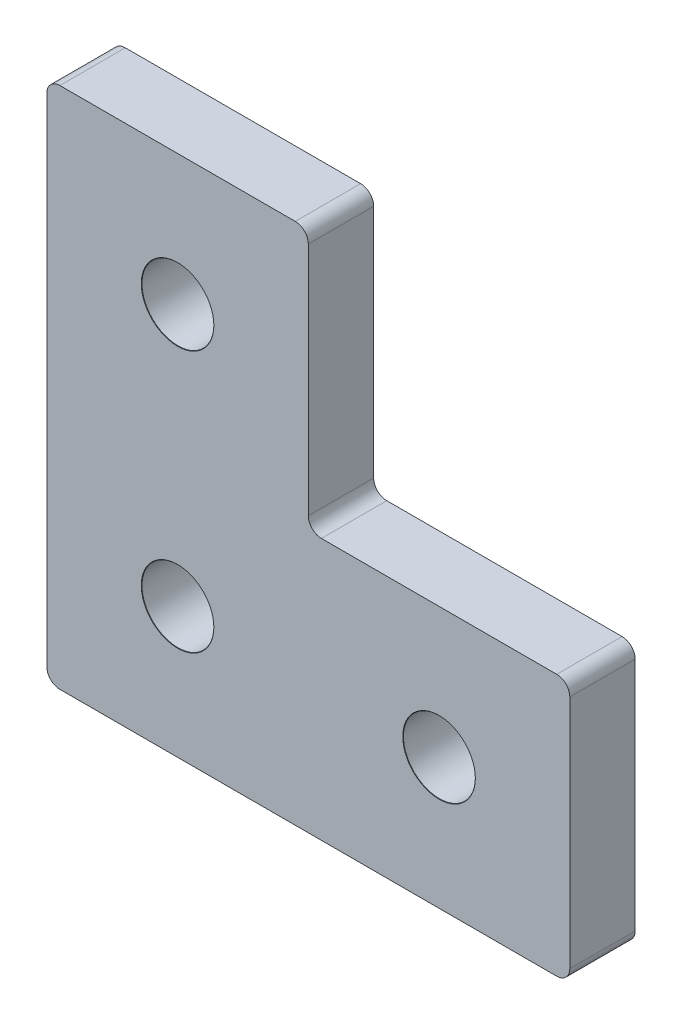
SolidWorks part; units mm, degrees
ref_plane "Front Plane" through (0, 0, 0) normal (0, 0, 1) x (1, 0, 0)
ref_plane "Top Plane" through (0, 0, 0) normal (0, 1, 0) x (1, 0, 0)
ref_plane "Right Plane" through (0, 0, 0) normal (1, 0, 0) x (0, 0, -1)
sketch "Sketch1" plane through (0, 0, 0) normal (0, 0, 1) x (1, 0, 0)
  line L0 (1, 0) -> (39, 0)
  line L2 (0, 1) -> (0, 39)
  line L3 (1, 40) -> (19, 40)
  line L5 (40, 1) -> (40, 19)
  line L6 (20, 39) -> (20, 21)
  line L7 (21, 20) -> (39, 20)
  arc A0 (1, 0) -> (0, 1) centre (1, 1) cw
  arc A1 (39, 0) -> (40, 1) centre (39, 1) ccw
  arc A2 (40, 19) -> (39, 20) centre (39, 19) ccw
  arc A3 (20, 21) -> (21, 20) centre (21, 21) ccw
  arc A4 (19, 40) -> (20, 39) centre (19, 39) cw
  arc A5 (0, 39) -> (1, 40) centre (1, 39) cw
  point P9 (0, 0)
  point P12 (40, 0)
  point P15 (40, 20)
  point P20 (20, 40)
  point P23 (0, 40)
  dimension "D4" = 1
  dimension "D1" = 20
  dimension "D2" = 40
  dimension "D3" = 20
extrude "Boss-Extrude1" add sketch "Sketch1" along normal blind 5
sketch "Sketch2" plane through (0, 0, 5) normal (0, 0, 1) x (1, 0, 0)
  line L0 (10, 40) -> (10, 0) construction
  line L1 (19, 40) -> (1, 40) construction
  line L2 (1, 0) -> (39, 0) construction
  line L3 (40, 10) -> (0, 10) construction
  line L4 (40, 1) -> (40, 19) construction
  line L5 (0, 39) -> (0, 1) construction
  point P12 (10, 30)
  point P13 (30, 10)
  point P14 (10, 10)
  dimension "D1" = 10
  dimension "D2" = 10
hole_wizard "M5 Clearance Hole1" positions "Sketch3" profile "Sketch4" hole size "M5" standard "ANSI Metric" end condition through all
sketch "Sketch3" plane through (0, 0, 5) normal (0, 0, 1) x (1, 0, 0)
  point P0 (10, 30)
  point P3 (10, 10)
  point P6 (30, 10)
sketch "Sketch4" plane through (10, 30, 5) normal (1, 0, 0) x (0, -1, 0)
  line L0 (0, 0) -> (0, 5)
  line L1 (0, 5) -> (2.75, 5)
  line L2 (2.75, 5) -> (2.75, 0.025)
  line L3 (2.75, 0.025) -> (2.775, 0)
  line L5 (2.775, 0) -> (0, 0)
  line L6 (-2.75, 0.025) -> (-2.775, 0) construction
  line L11 (0, -6.35) -> (0, 107.95) construction
  dimension "Thru Hole Dia." = 5.5
  dimension "Thru Hole Depth" = 5
  dimension "Near C'Sink Dia." = 5.55
  dimension "Near C'Sink Angle" = 90
